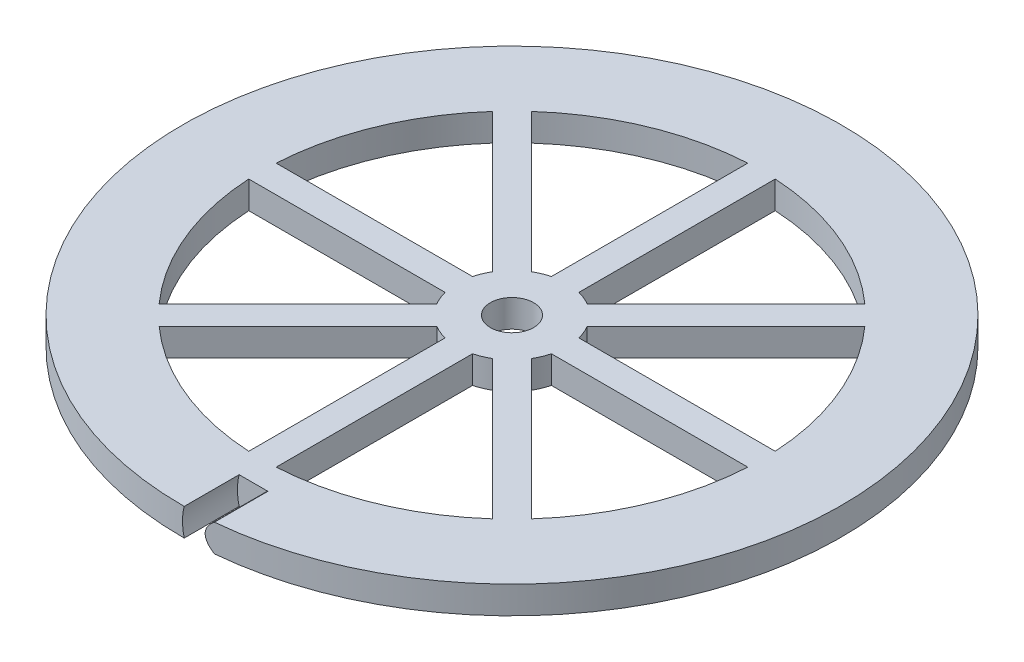
SolidWorks part; units mm, degrees
material "AISI 316 Stainless Steel Sheet (SS)"
ref_plane "Front Plane" through (0, 0, 0) normal (0, 0, 1) x (1, 0, 0)
ref_plane "Top Plane" through (0, 0, 0) normal (0, 1, 0) x (1, 0, 0)
ref_plane "Right Plane" through (0, 0, 0) normal (1, 0, 0) x (0, 0, -1)
sketch "Sketch1" plane through (0, 0, 0) normal (0, 1, 0) x (1, 0, 0)
  line L0 (-3.175, 57.6977) -> (-3.175, 12.2967)
  line L1 (3.175, 57.6977) -> (3.175, 12.2967)
  line L2 (38.5534, 43.0435) -> (6.45, 10.9402)
  line L3 (43.0435, 38.5534) -> (10.9402, 6.45)
  line L4 (57.6977, 3.175) -> (12.2967, 3.175)
  line L5 (57.6977, -3.175) -> (12.2967, -3.175)
  line L6 (43.0435, -38.5534) -> (10.9402, -6.45)
  line L7 (38.5534, -43.0435) -> (6.45, -10.9402)
  line L8 (3.175, -57.6977) -> (3.175, -12.2967)
  line L9 (-3.175, -57.6977) -> (-3.175, -12.2967)
  line L10 (-38.5534, -43.0435) -> (-6.45, -10.9402)
  line L11 (-43.0435, -38.5534) -> (-10.9402, -6.45)
  line L12 (-57.6977, -3.175) -> (-12.2967, -3.175)
  line L13 (-57.6977, 3.175) -> (-12.2967, 3.175)
  line L14 (-43.0435, 38.5534) -> (-10.9402, 6.45)
  line L15 (-38.5534, 43.0435) -> (-6.45, 10.9402)
  circle A0 centre (0, 0) radius 76.2
  circle A1 centre (0, 0) radius 5
  circle A2 centre (0, 0) radius 12.7
  circle A3 centre (0, 0) radius 57.785
  point P10 (-42.195, 55.6651)
  point P11 (0, 0)
  point P41 (0, 0)
  dimension "D1" = 152.4
  dimension "D2" = 115.57
  dimension "D3" = 10
  dimension "D4" = 25.4
  dimension "D5" = 6.35
  dimension "D6" = 8
extrude "Boss-Extrude1" add sketch "Sketch1" along normal mid plane 6.35 contours A0 A3 | L15 A3 L14 A2 | L13 A3 L12 A2 | L11 A3 L10 A2 | A2 A1 | L9 A3 L8 A2 | L7 A3 L6 A2 | L5 A3 L4 A2 | L3 A3 L2 A2 | L1 A3 L0 A2
ref_plane "Plane1" through (0, 0, 76.2) normal (0, 0, 1) x (1, 0, 0)
sketch "Sketch2" plane through (0, 0, 76.2) normal (0, 0, 1) x (1, 0, 0)
  line L0 (1.7015, 6.35) -> (4.4534, 11.1165) construction
  line L1 (1.7015, -6.35) -> (1.7015, 6.35) construction
  line L2 (1.7015, 6.35) -> (14.4015, 6.35)
  line L3 (1.7015, -6.35) -> (14.4015, -6.35)
  arc A0 (1.7015, 6.35) -> (1.7015, -6.35) centre (12.7, 0) ccw
  ellipse E0 centre (17.78, 0) end of major axis (-7.62, 0) minor radius 8.2026 (1.7015, -6.35) -> (1.7015, 6.35) cw construction
  ellipse E1 centre (30.48, 0) end of major axis (5.08, 0) minor radius 8.2026 (14.4015, -6.35) -> (14.4015, 6.35) cw
  point P5 (0, 0)
  point P15 (14.4015, -6.35)
  dimension "D1" = 30
  dimension "D2" = 12.7
  dimension "D3" = 5.08
  dimension "D5" = 12.7
  dimension "D6" = 25.4
  dimension "D4" = 2
extrude "Cut-Extrude1" cut sketch "Sketch2" against normal blind 12.7
